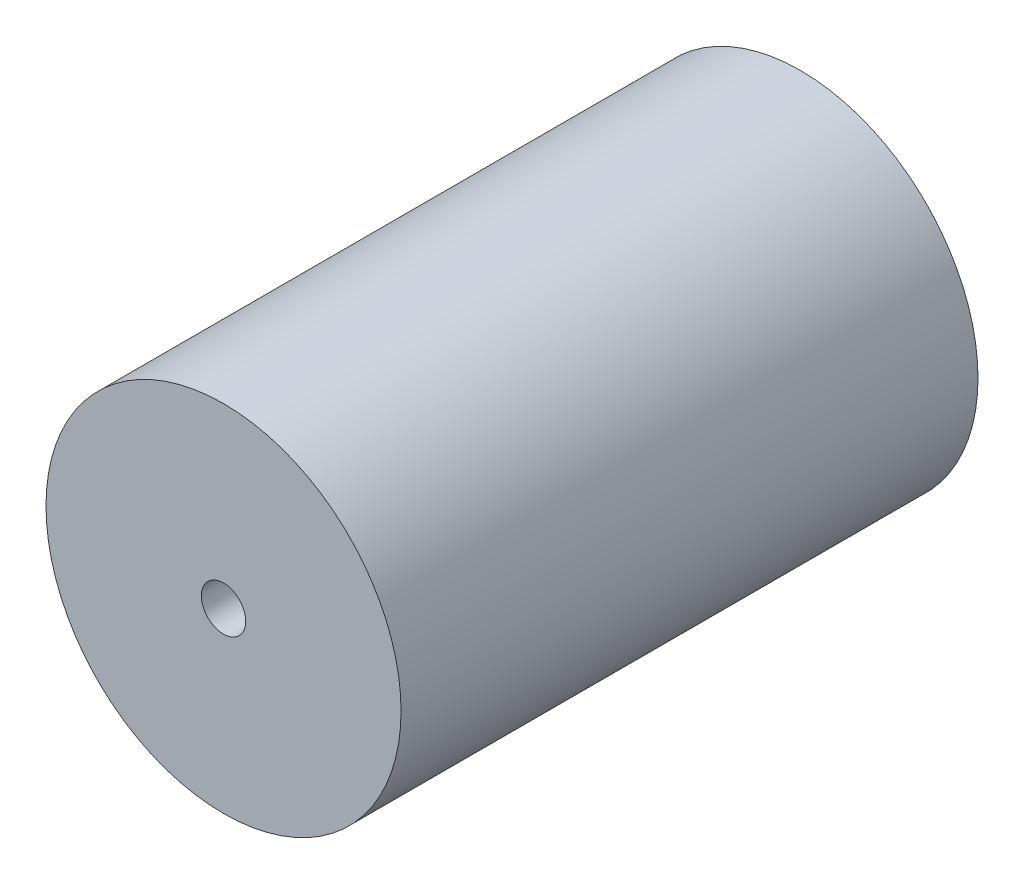
SolidWorks part; units mm, degrees
ref_plane "Front Plane" through (0, 0, 0) normal (0, 0, 1) x (1, 0, 0)
ref_plane "Top Plane" through (0, 0, 0) normal (0, 1, 0) x (1, 0, 0)
ref_plane "Right Plane" through (0, 0, 0) normal (1, 0, 0) x (0, 0, -1)
sketch "Sketch1" plane through (0, 0, 0) normal (0, 0, 1) x (1, 0, 0)
  circle A0 centre (0, 0) radius 2.6
  circle A1 centre (0, 0) radius 4
extrude "Boss-Extrude3" add sketch "Sketch1" along normal blind 11
sketch "Sketch3" plane through (0, 0, 11) normal (0, 0, 1) x (1, 0, 0)
  circle A0 centre (0, 0) radius 4
extrude "Boss-Extrude4" add sketch "Sketch3" along normal blind 2
sketch "Sketch4" plane through (0, 0, 13) normal (0, 0, 1) x (1, 0, 0)
  circle A0 centre (0, 0) radius 0.5
extrude "Cut-Extrude1" cut sketch "Sketch4" against normal blind 1
